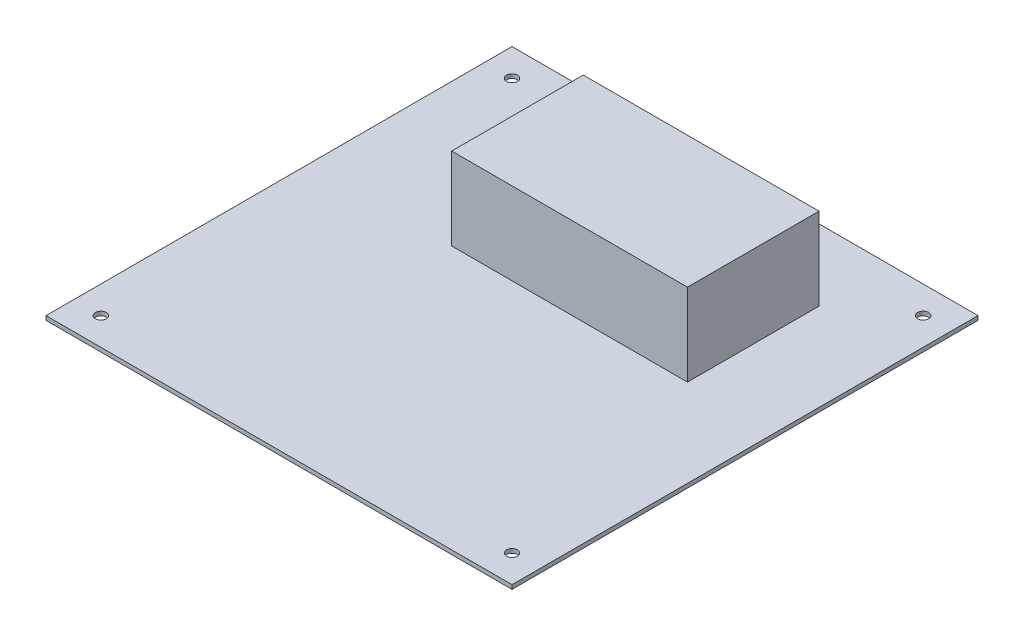
SolidWorks part; units mm, degrees
ref_plane "Front Plane" through (0, 0, 0) normal (0, 0, 1) x (1, 0, 0)
ref_plane "Top Plane" through (0, 0, 0) normal (0, 1, 0) x (1, 0, 0)
ref_plane "Right Plane" through (0, 0, 0) normal (1, 0, 0) x (0, 0, -1)
sketch "Sketch1" plane through (0, 0, 0) normal (0, 1, 0) x (1, 0, 0)
  line L1 (85, -85) -> (-85, -85)
  line L2 (85, -85) -> (85, 85)
  line L3 (85, 85) -> (-85, 85)
  line L4 (-85, -85) -> (-85, 85)
  line L5 (85, -85) -> (-85, 85) construction
  line L6 (85, 85) -> (-85, -85) construction
  line L7 (90, -90) -> (-90, -90)
  line L8 (90, -90) -> (90, 90)
  line L9 (90, 90) -> (-90, 90)
  line L10 (-90, -90) -> (-90, 90)
  line L11 (90, -90) -> (-90, 90) construction
  line L12 (90, 90) -> (-90, -90) construction
  circle A0 centre (-75, 75) radius 2
  circle A1 centre (75, 75) radius 2
  circle A3 centre (75, -75) radius 2
  circle A4 centre (-75, -75) radius 2
  point P0 (0, 0)
  point P5 (0, 0)
  dimension "D5" = 4
  dimension "D6" = 4
  dimension "D8" = 15
  dimension "D9" = 4
  dimension "D10" = 4
  dimension "D1" = 170
  dimension "D2" = 170
  dimension "D3" = 180
  dimension "D4" = 180
  dimension "D7" = 15
  dimension "D11" = 15
  dimension "D12" = 15
extrude "Boss-Extrude1" add sketch "Sketch1" along normal blind 1.5 contours L4 L1 L2 L3 A4 A3 A1 A0
sketch "Sketch2" plane through (0, 1.5, 0) normal (0, 1, 0) x (1, 0, 0)
  line L0 (-85, -85) -> (-85, 85) construction
  line L1 (53, 11) -> (-33, 11)
  line L2 (53, 11) -> (53, 59)
  line L3 (53, 59) -> (-33, 59)
  line L4 (-33, 11) -> (-33, 59)
  line L5 (53, 11) -> (-33, 59) construction
  line L6 (53, 59) -> (-33, 11) construction
  line L7 (85, 85) -> (-85, 85) construction
  point P0 (10, 35)
  dimension "D1" = 95
  dimension "D2" = 50
  dimension "D3" = 86
  dimension "D4" = 48
extrude "Boss-Extrude2" add sketch "Sketch2" along normal blind 30 contours L2 L1 L4 L3
